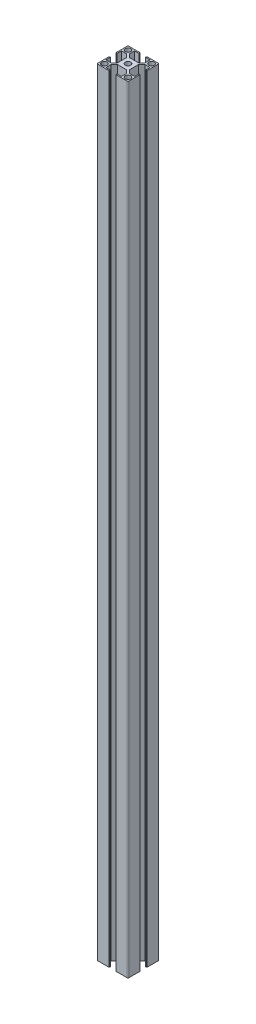
SolidWorks part; units mm, degrees
ref_plane "Front Plane" through (0, 0, 0) normal (0, 0, 1) x (1, 0, 0)
ref_plane "Top Plane" through (0, 0, 0) normal (0, 1, 0) x (1, 0, 0)
ref_plane "Right Plane" through (0, 0, 0) normal (1, 0, 0) x (0, 0, -1)
sketch "Sketch1" plane through (0, 0, 0) normal (0, 1, 0) x (1, 0, 0)
  line L0 (20, 19) -> (20, -19)
  line L1 (-19, -20) -> (19, -20)
  line L2 (-20, -19) -> (-20, 19)
  line L3 (-19, 20) -> (19, 20)
  line L5 (-20, -20) -> (20, 0) construction
  line L6 (-20, 20) -> (20, 0) construction
  line L7 (-20, 20) -> (20, -20) construction
  line L8 (20, 20) -> (-20, -20) construction
  line L9 (-20, 0) -> (20, 0) construction
  line L10 (-10, -18.5) -> (10, -18.5)
  line L11 (10, -18.5) -> (10, -11.825)
  line L12 (10, -11.825) -> (5.875, -7.7)
  line L13 (5.875, -7.7) -> (-5.875, -7.7)
  line L14 (-5.875, -7.7) -> (-10, -11.825)
  line L15 (-10, -11.825) -> (-10, -18.5)
  line L16 (-11.825, -10) -> (-18.5, -10)
  line L17 (-7.7, -5.875) -> (-11.825, -10)
  line L18 (-7.7, 5.875) -> (-7.7, -5.875)
  line L19 (-11.825, 10) -> (-7.7, 5.875)
  line L20 (-18.5, 10) -> (-11.825, 10)
  line L21 (-18.5, -10) -> (-18.5, 10)
  line L22 (-10, 11.825) -> (-10, 18.5)
  line L23 (-5.875, 7.7) -> (-10, 11.825)
  line L24 (5.875, 7.7) -> (-5.875, 7.7)
  line L25 (10, 11.825) -> (5.875, 7.7)
  line L26 (10, 18.5) -> (10, 11.825)
  line L27 (-10, 18.5) -> (10, 18.5)
  line L28 (0, 20) -> (0, -20) construction
  line L29 (18.5, -10) -> (18.5, 10)
  line L30 (18.5, 10) -> (11.825, 10)
  line L31 (11.825, 10) -> (7.7, 5.875)
  line L32 (7.7, 5.875) -> (7.7, -5.875)
  line L33 (7.7, -5.875) -> (11.825, -10)
  line L34 (11.825, -10) -> (18.5, -10)
  line L35 (15.1625, -10) -> (15.1625, -15.1625) construction
  arc A0 (-19, -20) -> (-20, -19) centre (-19, -19) cw
  arc A1 (20, -19) -> (19, -20) centre (19, -19) cw
  arc A2 (20, 19) -> (19, 20) centre (19, 19) ccw
  arc A3 (-19, 20) -> (-20, 19) centre (-19, 19) ccw
  circle A4 centre (15.1625, -15.1625) radius 3.5
  circle A5 centre (-15.1625, -15.1625) radius 3.5
  circle A6 centre (-15.1625, 15.1625) radius 3.5
  circle A7 centre (15.1625, 15.1625) radius 3.5
  circle A8 centre (0, 0) radius 3.5
  point P30 (0, 0)
  point P31 (0, 18.5)
  point P59 (0, 0)
  dimension "D7" = 1
  dimension "D8" = 7
  dimension "D10" = 7
  dimension "D1" = 40
  dimension "D2" = 40
  dimension "D3" = 10.8
  dimension "D4" = 11.75
  dimension "D5" = 20
  dimension "D6" = 1.5
  dimension "D9" = 4
extrude "Boss-Extrude1" add sketch "Sketch1" along normal blind 1000
sketch "Sketch2" plane through (0, 1000, 0) normal (0, 1, 0) x (1, 0, 0)
  line L0 (-4.65, 20) -> (-4.65, 19.35)
  line L1 (19, 20) -> (-19, 20) construction
  line L2 (-4.55, 19.25) -> (-4.25, 19.25)
  line L3 (-4.15, 19.15) -> (-4.15, 18.5)
  line L4 (10, 18.5) -> (-10, 18.5) construction
  line L5 (0, 20) -> (0, 18.5) construction
  line L6 (4.15, 19.15) -> (4.15, 18.5)
  line L7 (4.55, 19.25) -> (4.25, 19.25)
  line L8 (4.65, 20) -> (4.65, 19.35)
  line L9 (-4.65, 20) -> (4.65, 20)
  line L10 (-4.15, 18.5) -> (4.15, 18.5)
  line L11 (20, 4.65) -> (19.35, 4.65)
  line L12 (19.25, 4.55) -> (19.25, 4.25)
  line L13 (19.15, 4.15) -> (18.5, 4.15)
  line L14 (19.15, -4.15) -> (18.5, -4.15)
  line L15 (19.25, -4.55) -> (19.25, -4.25)
  line L16 (20, -4.65) -> (19.35, -4.65)
  line L17 (20, 4.65) -> (20, -4.65)
  line L18 (18.5, 4.15) -> (18.5, -4.15)
  line L19 (20, 0) -> (18.5, 0) construction
  line L20 (4.65, -20) -> (4.65, -19.35)
  line L21 (4.55, -19.25) -> (4.25, -19.25)
  line L22 (4.15, -19.15) -> (4.15, -18.5)
  line L23 (-4.15, -19.15) -> (-4.15, -18.5)
  line L24 (-4.55, -19.25) -> (-4.25, -19.25)
  line L25 (-4.65, -20) -> (-4.65, -19.35)
  line L26 (4.65, -20) -> (-4.65, -20)
  line L27 (4.15, -18.5) -> (-4.15, -18.5)
  line L28 (0, -20) -> (0, -18.5) construction
  line L29 (-20, -4.65) -> (-19.35, -4.65)
  line L30 (-19.25, -4.55) -> (-19.25, -4.25)
  line L31 (-19.15, -4.15) -> (-18.5, -4.15)
  line L32 (-19.15, 4.15) -> (-18.5, 4.15)
  line L33 (-19.25, 4.55) -> (-19.25, 4.25)
  line L34 (-20, 4.65) -> (-19.35, 4.65)
  line L35 (-20, -4.65) -> (-20, 4.65)
  line L36 (-18.5, -4.15) -> (-18.5, 4.15)
  line L37 (-20, 0) -> (-18.5, 0) construction
  arc A0 (4.55, 19.25) -> (4.65, 19.35) centre (4.55, 19.35) ccw
  arc A1 (4.25, 19.25) -> (4.15, 19.15) centre (4.25, 19.15) ccw
  arc A2 (-4.15, 19.15) -> (-4.25, 19.25) centre (-4.25, 19.15) ccw
  arc A3 (-4.65, 19.35) -> (-4.55, 19.25) centre (-4.55, 19.35) ccw
  arc A4 (19.25, -4.55) -> (19.35, -4.65) centre (19.35, -4.55) ccw
  arc A5 (19.25, -4.25) -> (19.15, -4.15) centre (19.15, -4.25) ccw
  arc A6 (19.15, 4.15) -> (19.25, 4.25) centre (19.15, 4.25) ccw
  arc A7 (19.35, 4.65) -> (19.25, 4.55) centre (19.35, 4.55) ccw
  arc A8 (-4.55, -19.25) -> (-4.65, -19.35) centre (-4.55, -19.35) ccw
  arc A9 (-4.25, -19.25) -> (-4.15, -19.15) centre (-4.25, -19.15) ccw
  arc A10 (4.15, -19.15) -> (4.25, -19.25) centre (4.25, -19.15) ccw
  arc A11 (4.65, -19.35) -> (4.55, -19.25) centre (4.55, -19.35) ccw
  arc A12 (-19.25, 4.55) -> (-19.35, 4.65) centre (-19.35, 4.55) ccw
  arc A13 (-19.25, 4.25) -> (-19.15, 4.15) centre (-19.15, 4.25) ccw
  arc A14 (-19.15, -4.15) -> (-19.25, -4.25) centre (-19.15, -4.25) ccw
  arc A15 (-19.35, -4.65) -> (-19.25, -4.55) centre (-19.35, -4.55) ccw
  point P16 (4.65, 19.25)
  point P19 (4.15, 19.25)
  point P22 (-4.15, 19.25)
  point P25 (-4.65, 19.25)
  point P83 (0, 0)
  dimension "D4" = 0.1
  dimension "D1" = 0.75
  dimension "D2" = 0.5
  dimension "D3" = 4.15
  dimension "D5" = 4
extrude "Cut-Extrude1" cut sketch "Sketch2" against normal through all
